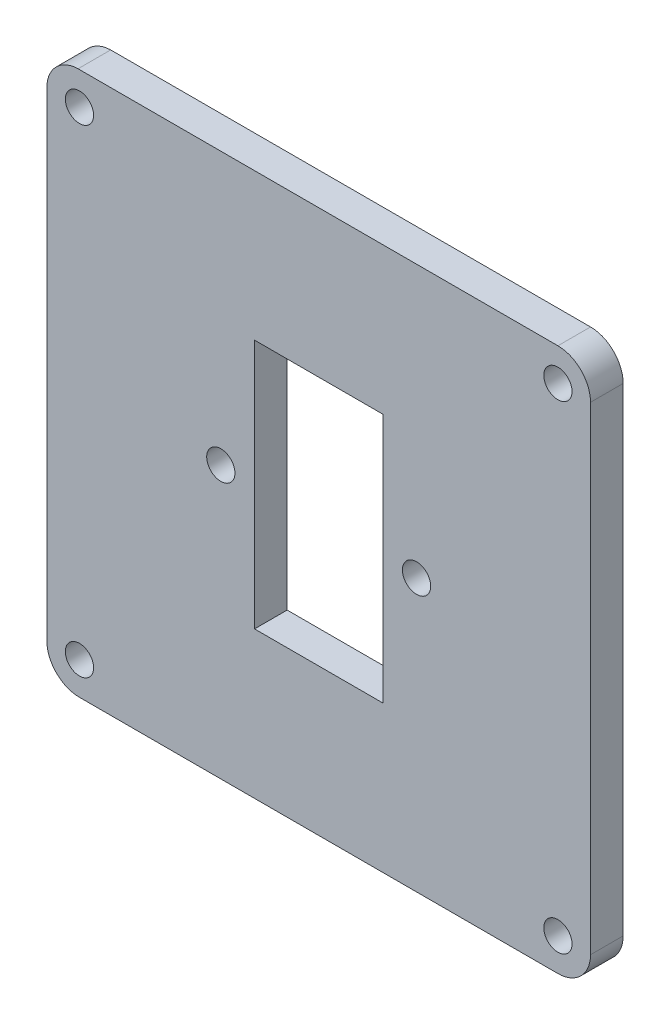
SolidWorks part; units mm, degrees
ref_plane "Front Plane" through (0, 0, 0) normal (0, 0, 1) x (1, 0, 0)
ref_plane "Top Plane" through (0, 0, 0) normal (0, 1, 0) x (1, 0, 0)
ref_plane "Right Plane" through (0, 0, 0) normal (1, 0, 0) x (0, 0, -1)
sketch "Model" plane through (0, 0, 0) normal (0, 0, 1) x (1, 0, 0)
  line L0 (33.3225, 20.1297) -> (33.3225, 64.1296)
  line L1 (52.4225, 53.6296) -> (64.2225, 53.6296)
  line L2 (52.4225, 30.6296) -> (64.2225, 30.6296)
  line L3 (80.3225, 17.1296) -> (36.3225, 17.1296)
  line L4 (83.3225, 64.1296) -> (83.3225, 20.1297)
  line L5 (64.2225, 53.6296) -> (64.2225, 30.6296)
  line L6 (52.4225, 30.6296) -> (52.4225, 53.6296)
  line L7 (36.1917, 67.1268) -> (80.3225, 67.1296)
  circle A0 centre (36.3225, 64.1297) radius 1.3
  circle A1 centre (80.3225, 64.1297) radius 1.3
  circle A2 centre (67.3225, 42.1296) radius 1.3
  circle A3 centre (49.3224, 42.1297) radius 1.3
  circle A4 centre (36.3225, 20.1296) radius 1.3
  circle A5 centre (80.3225, 20.1296) radius 1.3
  arc A6 (33.3225, 20.1297) -> (36.3225, 17.1296) centre (36.3224, 20.1295) ccw
  arc A7 (36.1917, 67.1268) -> (33.3225, 64.1296) centre (36.2554, 64.1938) ccw
  arc A8 (83.3225, 64.1296) -> (80.3225, 67.1296) centre (80.3226, 64.1297) ccw
  arc A9 (80.3225, 17.1296) -> (83.3225, 20.1297) centre (80.3224, 20.1297) ccw
extrude "Boss-Extrude1" add sketch "Model" along normal blind 3
